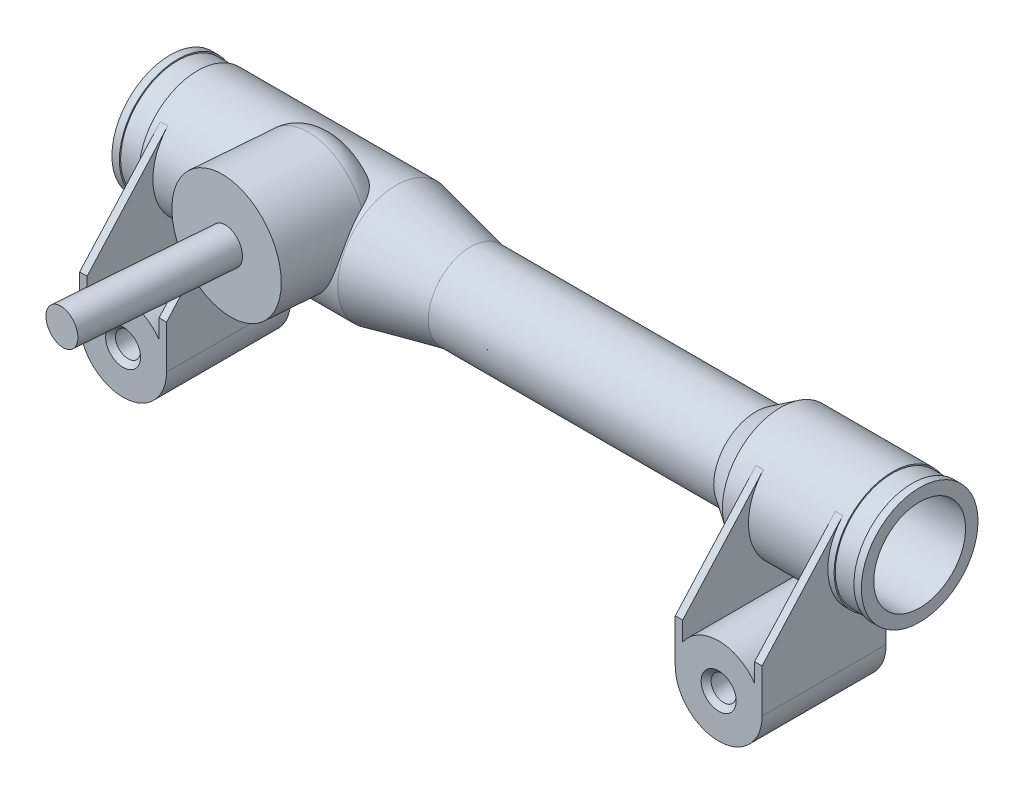
SolidWorks part; units mm, degrees
material "0.6015 (EN-GJL-150)"
ref_plane "Płaszczyzna przednia" through (0, 0, 0) normal (0, 0, 1) x (1, 0, 0)
ref_plane "Płaszczyzna górna" through (0, 0, 0) normal (0, 1, 0) x (1, 0, 0)
ref_plane "Płaszczyzna prawa" through (0, 0, 0) normal (1, 0, 0) x (0, 0, -1)
sketch "Szkic1" plane through (0, 0, 0) normal (1, 0, 0) x (0, 0, -1)
  circle A0 centre (0, 0) radius 23.5
  dimension "D1" = 47
extrude "Dodanie-wyciągnięcie1" add sketch "Szkic1" along normal blind 302
ref_plane "Płaszczyzna1" through (0, 23.5, 0) normal (0, 1, 0) x (1, 0, 0)
sketch "Szkic3" plane through (0, 23.5, 0) normal (0, 1, 0) x (1, 0, 0)
  line L0 (0, 0) -> (302, 0) construction
  line L1 (302, -23.5) -> (302, 23.5) construction
sketch "Szkic2" plane through (0, 0, 0) normal (0, 0, 1) x (1, 0, 0)
  line L1 (302, 23.5) -> (0, 23.5) construction
  line L2 (151, -23.5) -> (151, 41.5869) construction
  line L3 (0, -23.5) -> (302, -23.5) construction
  circle A0 centre (31, -38) radius 17.5
  dimension "D1" = 35
  dimension "D2" = 120
  dimension "D3" = 61.5
extrude "Dodanie-wyciągnięcie2" add sketch "Szkic2" along normal blind 50
sketch "Szkic4" plane through (0, 0, 0) normal (0, 0, -1) x (-1, 0, 0)
  line L0 (-31, -38) -> (-323.956, -38) construction
  circle A0 centre (-271, -38) radius 17.5
  circle A1 centre (-31, -38) radius 17.5 construction
  dimension "D1" = 240
  dimension "D2" = 35
extrude "Dodanie-wyciągnięcie3" add sketch "Szkic4" against normal blind 50
sketch "Szkic5" plane through (0, 0, 50) normal (0, 0, 1) x (1, 0, 0)
  circle A0 centre (31, -38) radius 5.05
  circle A1 centre (271, -38) radius 5.05
  dimension "D1" = 10.1
  dimension "D2" = 10.1
extrude "Wytnij-wyciągnięcie1" cut sketch "Szkic5" against normal blind 50
chamfer "Sfazowanie1" distance 2 angle 45 4 edges at (36.05, -38, 0) (276.05, -38, 0) (276.05, -38, 50) (36.05, -38, 50)
sketch "Szkic7" plane through (0, 23.5, 0) normal (0, 1, 0) x (1, 0, 0)
  line L0 (68, 0) -> (64.6945, -42) construction
  line L1 (0, 0) -> (302, 0) construction
  line L2 (0, 23.5) -> (0, -23.5) construction
  line L3 (68, 0) -> (68, -42) construction
  dimension "D1" = 68
  dimension "D2" = 4.5
  dimension "D3" = 42
ref_plane "Płaszczyzna2" through (0, -55.5, 0) normal (0, -1, 0) x (-1, 0, 0)
ref_plane "Płaszczyzna3" through (64.6945, 23.5, 42) normal (-0.0785, 0, 0.9969) x (0.9969, 0, 0.0785)
sketch "Szkic8" plane through (64.6945, 23.5, 42) normal (-0.0785, 0, 0.9969) x (0.9969, 0, 0.0785)
  line L0 (0, 0) -> (0, -79) construction
  line L1 (-95.726, -79) -> (-39.8548, -79) construction
  circle A0 centre (0, -13.25) radius 24
  dimension "D2" = 48
  dimension "D1" = 65.75
extrude "Dodanie-wyciągnięcie4" add sketch "Szkic8" against normal up to vertex (42.1299 mm away) up to point (68, 23.5, 0)
sketch "Szkic10" plane through (0, 0, 0) normal (-1, 0, 0) x (0, 0, 1)
  line L0 (23.5, 0) -> (103.5, 0) construction
  circle A0 centre (0, 0) radius 23.5 construction
  dimension "D1" = 80
sketch "Szkic11" plane through (0, 23.5, 0) normal (0, 1, 0) x (1, 0, 0)
  line L0 (64.6945, -42) -> (59.8544, -103.5) construction
  line L1 (68, 0) -> (64.6945, -42) construction
  dimension "D1" = 61.6902
sketch "Szkic12" plane through (-2.8869, 0, 36.6812) normal (-0.0785, 0, 0.9969) x (0.9969, 0, 0.0785)
  circle A0 centre (67.7904, 10.25) radius 7
  dimension "D1" = 14
extrude "Dodanie-wyciągnięcie5" add sketch "Szkic12" along normal up to vertex (61.6902 mm away) up to point (59.8544, 23.5, 103.5)
sketch "Szkic6" plane through (0, 0, 0) normal (-1, 0, 0) x (0, 0, 1)
  circle A0 centre (0, 0) radius 11
  dimension "D1" = 22
extrude "Wytnij-wyciągnięcie2" cut sketch "Szkic6" against normal up to surface (302 mm away) up to face at (302, 0, -23.5)
sketch "Szkic13" plane through (64.6945, 23.5, 42) normal (-0.0785, 0, 0.9969) x (0.9969, 0, 0.0785)
  circle A0 centre (0, -13.25) radius 7
extrude "Dodanie-wyciągnięcie6" add sketch "Szkic13" against normal blind 50
sketch "Szkic14" plane through (0, 0, 0) normal (0, 0, 1) x (1, 0, 0)
  line L0 (151, 23.5) -> (151, -7.2498) construction
  line L1 (0, 23.5) -> (302, 23.5) construction
sketch "Szkic15" plane through (0, 0, 50) normal (0, 0, 1) x (1, 0, 0)
  line L0 (31, -20.5) -> (31, -55.5) construction
  line L1 (-27.5, -55.5) -> (27.5, -55.5) construction
  circle A0 centre (31, -38) radius 17.5 construction
ref_plane "Płaszczyzna4" through (31, 0, 0) normal (-1, 0, 0) x (0, 0, 1)
sketch "Szkic16" plane through (31, 0, 0) normal (-1, 0, 0) x (0, 0, 1)
  line L0 (50, -38) -> (0, -38)
  line L2 (50, -20.5) -> (50, -55.5) construction
  line L3 (0, -30.95) -> (0, -45.05) construction
  line L4 (0, -38) -> (0, -20.1726)
  line L5 (0, -20.1726) -> (13.8493, -17.0601)
  line L6 (13.8493, -17.0601) -> (21.5807, -1.9195)
  line L7 (21.5807, -1.9195) -> (17.4833, 15.7031)
  line L9 (0, -23.5) -> (0, -55.5) construction
  line L10 (50, -38) -> (50, -20.5)
  line L11 (50, -20.5) -> (11.4891, -20.5) construction
  line L12 (50, -20.5) -> (17.4833, 15.7031)
  circle A0 centre (0, 0) radius 23.5 construction
extrude "Dodanie-wyciągnięcie7" add sketch "Szkic16" along normal blind 3 from offset 14.5
fillet "Zaokrąglenie1" radius 10 1 edges at (68, 34.25, 0)
mirror "Lustro1" about plane through (31, 0, 0) normal (-1, 0, 0) of "Dodanie-wyciągnięcie7"
ref_plane "Płaszczyzna5" through (151, 0, 0) normal (-1, 0, 0) x (0, 0, 1)
mirror "Lustro2" about plane through (151, 0, 0) normal (-1, 0, 0) of "Dodanie-wyciągnięcie7", "Lustro1"
sketch "Szkic17" plane through (0, 0, 0) normal (-1, 0, 0) x (0, 0, 1)
  circle A0 centre (0, 0) radius 23.5
  circle A1 centre (0, 0) radius 23
  circle A2 centre (0, 0) radius 23.5 construction
  dimension "D1" = 46
extrude "Wytnij-wyciągnięcie3" cut sketch "Szkic17" against normal blind 8 from offset 3 offset against normal yes
mirror "Lustro3" about plane through (151, 0, 0) normal (-1, 0, 0) of "Wytnij-wyciągnięcie3"
sketch "Szkic18" plane through (151, 0, 0) normal (-1, 0, 0) x (0, 0, 1)
  circle A0 centre (0, 0) radius 23.5
  circle A1 centre (0, 0) radius 23.5 construction
  circle A2 centre (0, 0) radius 17
  dimension "D1" = 34
extrude "Wytnij-wyciągnięcie4" cut sketch "Szkic18" along normal blind 60 and the other way blind 95
sketch "Szkic19" plane through (0, 0, 0) normal (0, 0, 1) x (1, 0, 0)
  line L0 (91, 23.5) -> (91, 17)
  line L1 (91, 17) -> (121, 17)
  line L2 (246, 17) -> (91, 17) construction
  line L3 (121, 17) -> (91, 23.5)
  line L4 (246, 17) -> (246, 23.5)
  line L5 (246, 23.5) -> (236, 17)
  line L6 (236, 17) -> (246, 17)
  line L7 (0, 0) -> (302, 0) construction
  line L8 (302, -23.5) -> (302, 23.5) construction
  dimension "D1" = 30
  dimension "D2" = 10
revolve "Obrót1" add sketch "Szkic19" angle 360 about L7
sketch "Szkic20" plane through (0, 0, 0) normal (-1, 0, 0) x (0, 0, 1)
  circle A0 centre (0, 0) radius 18.5
  dimension "D1" = 37
extrude "Wytnij-wyciągnięcie5" cut sketch "Szkic20" against normal blind 45
mirror "Lustro4" about plane through (151, 0, 0) normal (-1, 0, 0) of "Wytnij-wyciągnięcie5"
